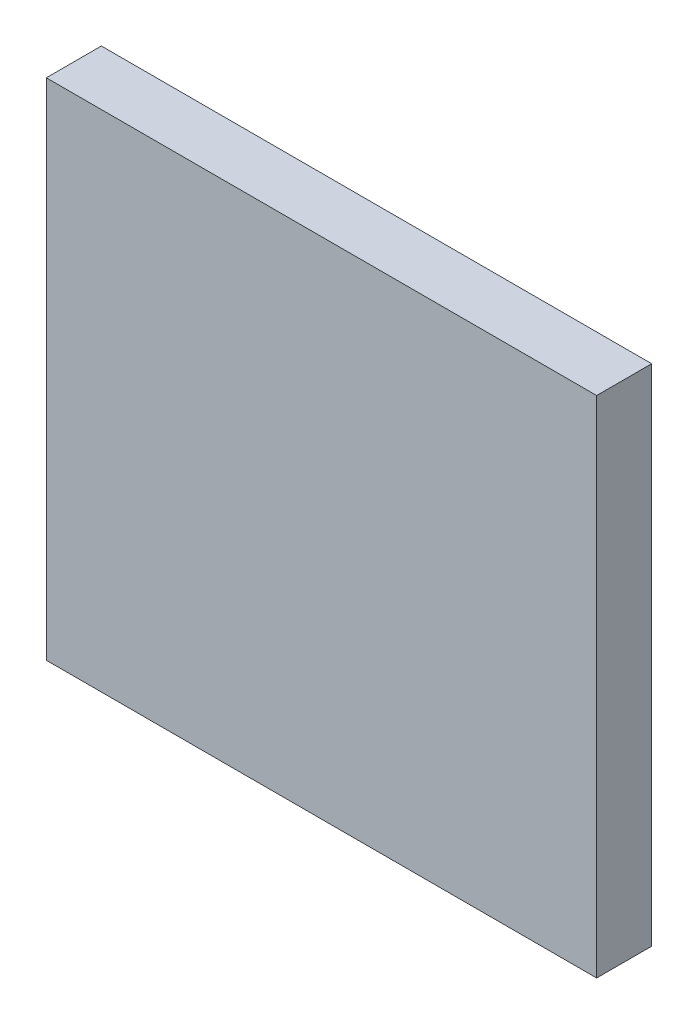
SolidWorks part; units mm, degrees
ref_plane "정면" through (0, 0, 0) normal (0, 0, 1) x (1, 0, 0)
ref_plane "윗면" through (0, 0, 0) normal (0, 1, 0) x (1, 0, 0)
ref_plane "우측면" through (0, 0, 0) normal (1, 0, 0) x (0, 0, -1)
sketch "Sketch1" plane through (0, 0, 0) normal (0, 0, 1) x (1, 0, 0)
  line L0 (0, -38.5988) -> (0, 26.9958) construction
  line L1 (30, 19.716) -> (-30, 19.716)
  line L2 (-30, 19.716) -> (-30, -35.284)
  line L3 (-30, -35.284) -> (30, -35.284)
  line L4 (30, 19.716) -> (30, -35.284)
  point P7 (0, 0)
  point P8 (0, -38.5988)
  point P10 (0, -35.284)
  point P11 (0, 19.716)
  dimension "D1" = 30
  dimension "D2" = 55
extrude "Boss-Extrude1" add sketch "Sketch1" along normal blind 6
